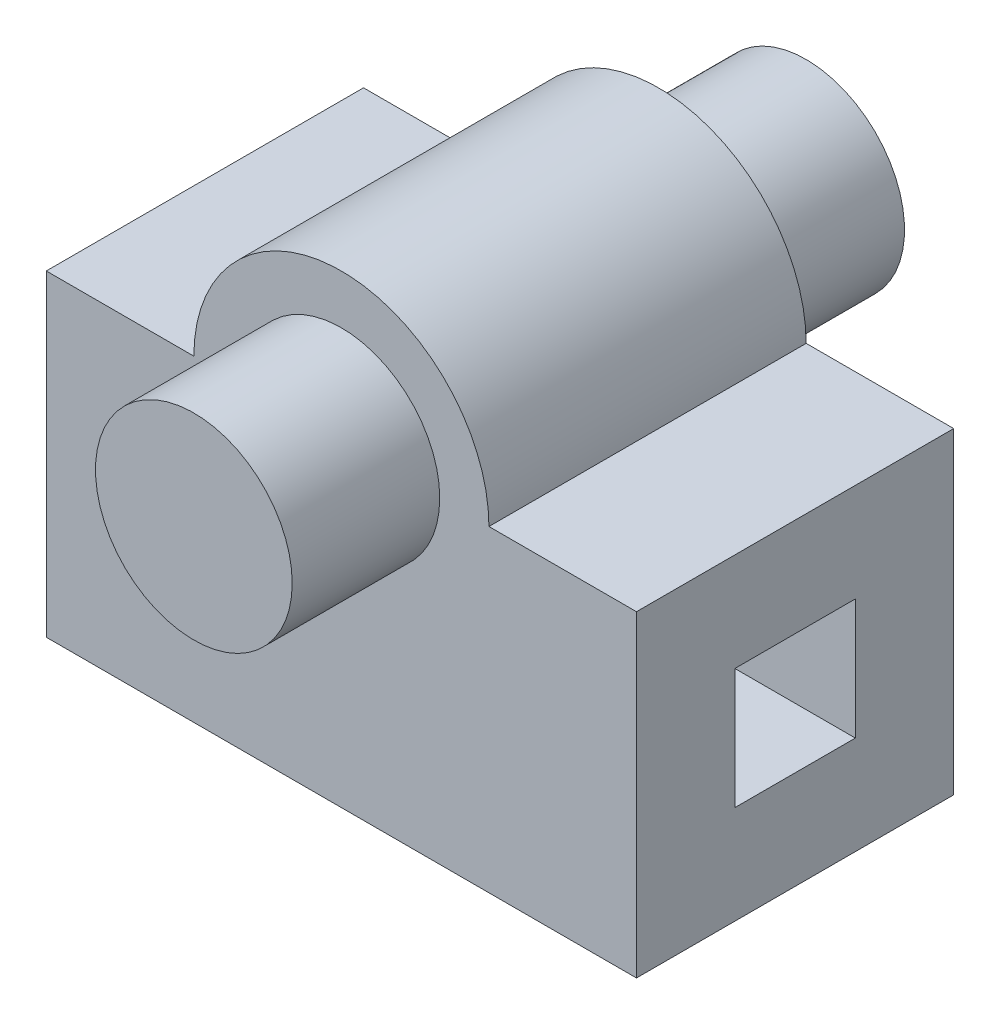
SolidWorks part; units mm, degrees
ref_plane "Front" through (0, 0, 0) normal (0, 0, 1) x (1, 0, 0)
ref_plane "Top" through (0, 0, 0) normal (0, 1, 0) x (1, 0, 0)
ref_plane "Right" through (0, 0, 0) normal (1, 0, 0) x (0, 0, -1)
sketch "草图1" plane through (0, 0, 0) normal (0, 1, 0) x (1, 0, 0)
  line L1 (-60, 32.25) -> (60, 32.25)
  line L2 (-60, 32.25) -> (-60, -32.25)
  line L3 (-60, -32.25) -> (60, -32.25)
  line L4 (60, 32.25) -> (60, -32.25)
  line L5 (-60, 32.25) -> (60, -32.25) construction
  line L6 (-60, -32.25) -> (60, 32.25) construction
  point P0 (0, 0)
  dimension "D1" = 64.5
  dimension "D2" = 120
extrude "凸台-拉伸1" add sketch "草图1" along normal blind 44.5
sketch "草图2" plane through (60, 0, 0) normal (1, 0, 0) x (0, 0, -1)
  line L0 (-32.25, 0) -> (32.25, 0) construction
  line L1 (-12.25, 0) -> (12.25, 0)
  line L2 (-12.25, 0) -> (-12.25, 24.5)
  line L3 (-12.25, 24.5) -> (12.25, 24.5)
  line L4 (12.25, 0) -> (12.25, 24.5)
  line L5 (-32.25, 44.5) -> (-32.25, 0) construction
  dimension "D1" = 24.5
  dimension "D2" = 24.5
  dimension "D3" = 20
  dimension "D4" = 24.5
extrude "切除-拉伸1" cut sketch "草图2" against normal through all
sketch "草图3" plane through (0, 0, 32.25) normal (0, 0, 1) x (1, 0, 0)
  line L0 (-60, 44.5) -> (60, 44.5) construction
  line L1 (-30, 44.5) -> (30, 44.5)
  arc A0 (30, 44.5) -> (-30, 44.5) centre (0, 44.5) ccw
  dimension "D1" = 60
extrude "凸台-拉伸2" add sketch "草图3" against normal blind 64.5
sketch "草图4" plane through (0, 0, 32.25) normal (0, 0, 1) x (1, 0, 0)
  circle A0 centre (0, 44.5) radius 20
  dimension "D1" = 40
extrude "凸台-拉伸3" add sketch "草图4" along normal blind 30
sketch "草图5" plane through (0, 0, -32.25) normal (0, 0, -1) x (-1, 0, 0)
  circle A0 centre (0, 44.5) radius 20
  dimension "D1" = 40
extrude "凸台-拉伸4" add sketch "草图5" along normal blind 30
sketch "草图6" plane through (60, 0, 0) normal (1, 0, 0) x (0, 0, -1)
  line L1 (-32.25, 0) -> (32.25, 0)
  line L2 (-32.25, 0) -> (-32.25, -20)
  line L3 (-32.25, -20) -> (32.25, -20)
  line L4 (32.25, 0) -> (32.25, -20)
  dimension "D1" = 64.5
  dimension "D2" = 20
extrude "凸台-拉伸5" add sketch "草图6" against normal blind 120
